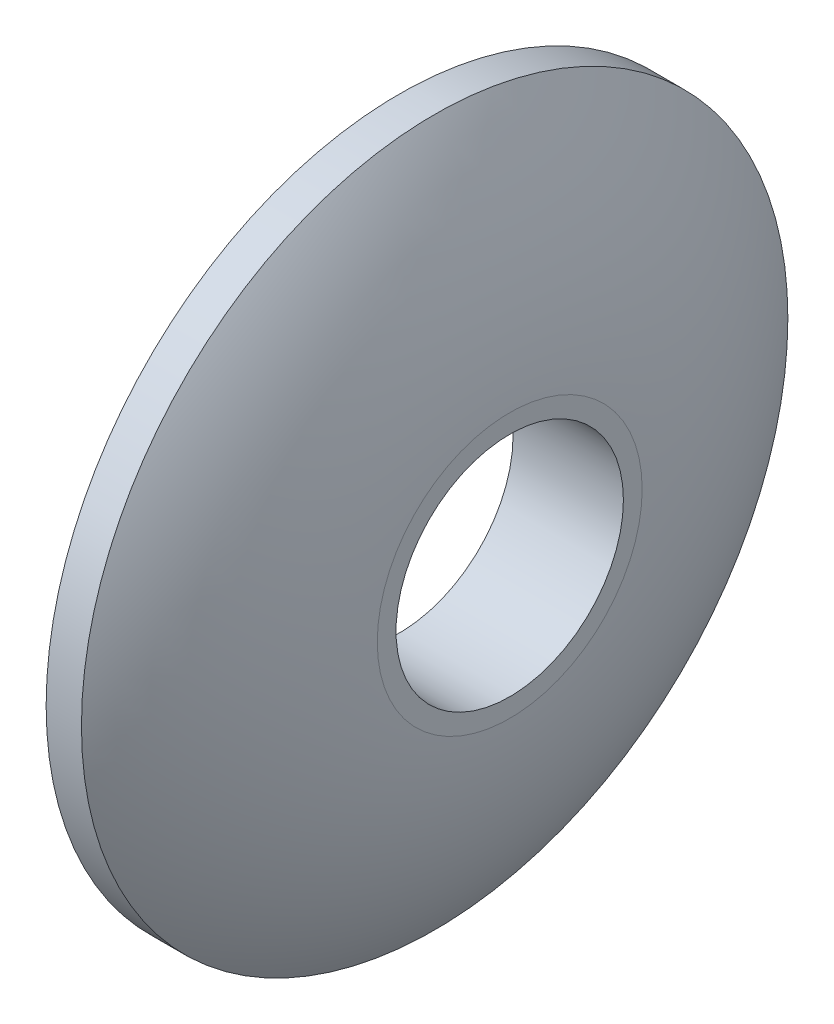
SolidWorks part; units mm, degrees
ref_plane "Front Plane" through (0, 0, 0) normal (0, 0, 1) x (1, 0, 0)
ref_plane "Top Plane" through (0, 0, 0) normal (0, 1, 0) x (1, 0, 0)
ref_plane "Right Plane" through (0, 0, 0) normal (1, 0, 0) x (0, 0, -1)
sketch "Sketch1" plane through (0, 0, 0) normal (0, 0, 1) x (1, 0, 0)
  line L0 (-13.2766, 0) -> (17.0213, 0) construction
  line L3 (0, 0) -> (0, 8)
  line L7 (2.5, 3) -> (2.5, 0)
  line L8 (2.5, 0) -> (0, 0)
  line L9 (0, 8) -> (0.8, 8)
  arc A0 (0.8, 8) -> (2.5, 3) centre (-7.4817, 2.3952) cw
  dimension "D4" = 10
  dimension "D1" = 8
  dimension "D2" = 2.5
  dimension "D3" = 5
  dimension "D5" = 1.7
revolve "Revolve1" add sketch "Sketch1" angle 360 about L0
sketch "Sketch2" plane through (2.5, 0, 0) normal (1, 0, 0) x (0, 0, -1)
  line L2 (-0.25, 2.2361) -> (-0.25, 2.4861)
  line L3 (-0.25, 2.4861) -> (0.25, 2.4861)
  line L4 (0.25, 2.2361) -> (0.25, 2.4861)
  line L5 (0, 2.25) -> (0.25, 2.4861) construction
  line L6 (-0.25, 2.4861) -> (0, 2.25) construction
  arc A0 (-0.25, 2.2361) -> (0.25, 2.2361) centre (0, 0) ccw
  point P3 (0, 2.25)
  dimension "D1" = 4.5
  dimension "D2" = 0.5
  dimension "D3" = 0.25
  dimension "D4" = 0.0139
extrude "Cut-Extrude1" [suppressed] cut sketch "Sketch2" against normal through all
sketch "Sketch5" plane through (2.5, 0, 0) normal (1, 0, 0) x (0, 0, -1)
  circle A0 centre (0, 0) radius 2.575
  dimension "D1" = 5.15
extrude "Cut-Extrude3" cut sketch "Sketch5" against normal through all
sketch "Sketch4" plane through (2.5, 0, 0) normal (1, 0, 0) x (0, 0, -1)
  circle A0 centre (0, 0) radius 3
  dimension "D1" = 6
extrude "Cut-Extrude2" [suppressed] cut sketch "Sketch4" against normal blind 0.5
